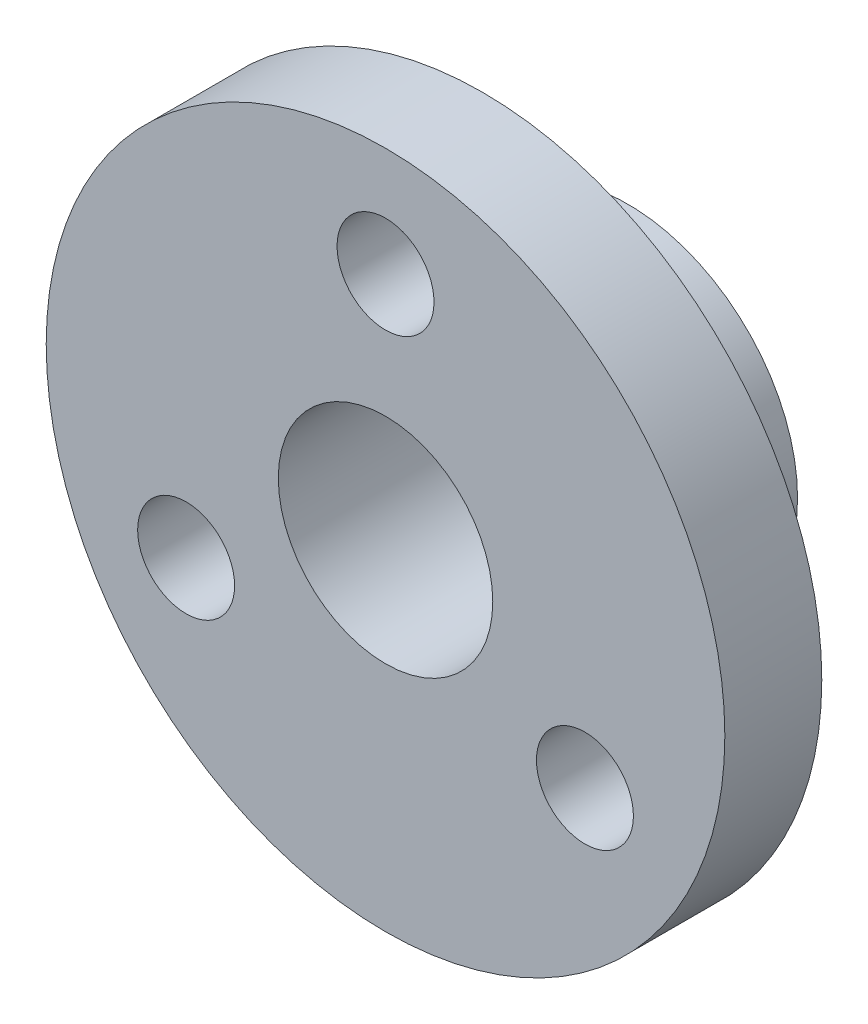
SolidWorks part; units mm, degrees
material "ABS"
ref_plane "Ön Düzlem" through (0, 0, 0) normal (0, 0, 1) x (1, 0, 0)
ref_plane "Üst Düzlem" through (0, 0, 0) normal (0, 1, 0) x (1, 0, 0)
ref_plane "Sağ Düzlem" through (0, 0, 0) normal (1, 0, 0) x (0, 0, -1)
sketch "Çizim1" plane through (0, 0, 0) normal (0, 0, 1) x (1, 0, 0)
  circle A0 centre (-30.7119, -38.9048) radius 2.2124
  circle A1 centre (-30.7119, -38.9048) radius 7
extrude "Yükseklik-Ekstrüzyon1" add sketch "Çizim1" along normal blind 2
sketch "Çizim2" plane through (0, 0, 2) normal (0, 0, 1) x (1, 0, 0)
  circle A0 centre (-30.7119, -38.9048) radius 2.2124
  circle A1 centre (-30.7119, -38.9048) radius 3.5
extrude "Yükseklik-Ekstrüzyon2" add sketch "Çizim2" against normal blind 5
sketch "Çizim3" plane through (0, 0, 0) normal (0, 0, -1) x (-1, 0, 0)
  circle A0 centre (30.7119, -38.9048) radius 4.75 construction
  circle A1 centre (30.7119, -34.1548) radius 1
  circle A2 centre (34.8255, -41.2798) radius 1
  circle A3 centre (26.5983, -41.2798) radius 1
  point P11 (30.7119, -38.9048)
  dimension "D1" = 3
extrude "Kes-Ekstrüzyon1" cut sketch "Çizim3" against normal blind 5
scale "Scale1" bodies to scale 103 scale about centroid uniform scaling yes scale factor 0.666667
